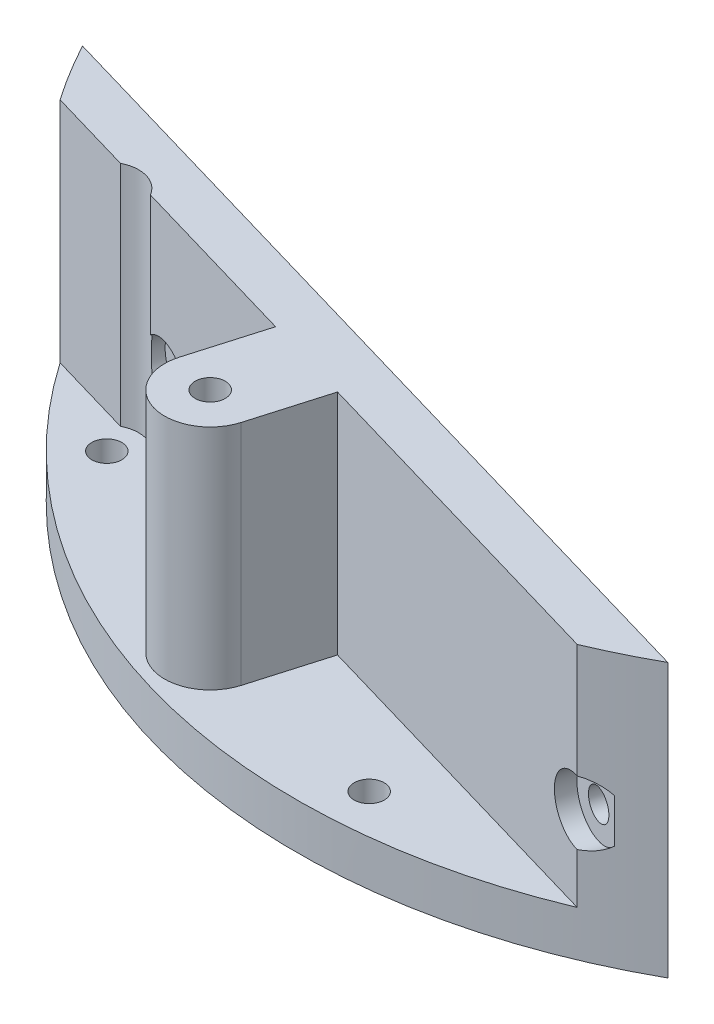
SolidWorks part; units mm, degrees
ref_plane "Front Plane" through (0, 0, 0) normal (0, 0, 1) x (1, 0, 0)
ref_plane "Top Plane" through (0, 0, 0) normal (0, 1, 0) x (1, 0, 0)
ref_plane "Right Plane" through (0, 0, 0) normal (1, 0, 0) x (0, 0, -1)
sketch "Sketch1" plane through (0, 0, 0) normal (0, 1, 0) x (1, 0, 0)
  line L0 (41.3804, -52.1206) -> (62.9195, 21.6805)
  line L1 (0, 0) -> (0, 66.55) construction
  line L2 (32.7481, -57.935) -> (-58.7697, -31.2253)
  line L3 (0, 0) -> (-47.058, -47.058) construction
  line L4 (0, 0) -> (0, -66.55) construction
  line L5 (0, 0) -> (3.483, -66.4588) construction
  circle A0 centre (0, 0) radius 66.55
  circle A2 centre (3.2213, -61.4656) radius 1.65
  circle A3 centre (-43.5224, -43.5224) radius 1.65
  dimension "D1" = 133.1
  dimension "D7" = 61.55
  dimension "D8" = 61.55
  dimension "D9" = 3.3
  dimension "D10" = 3.3
  dimension "D2" = 76.88
  dimension "D3" = 16.27
  dimension "D4" = 90
  dimension "D5" = 8
  dimension "D6" = 3
extrude "Boss-Extrude1" add sketch "Sketch1" along normal blind 5 contours L2 A0 A3 A2
sketch "Sketch2" plane through (0, 5, 0) normal (0, 1, 0) x (1, 0, 0)
  line L0 (-58.7697, -31.2253) -> (32.7481, -57.935)
  line L1 (-40.494, -41.7677) -> (26.121, -61.2095)
  line L2 (-54.9442, -37.5504) -> (-45.1316, -40.4143)
  arc A0 (26.121, -61.2095) -> (32.7481, -57.935) centre (0, 0) ccw
  arc A1 (-58.7697, -31.2253) -> (-54.9442, -37.5504) centre (0, 0) ccw
  arc A2 (-40.494, -41.7677) -> (-45.1316, -40.4143) centre (-43.5224, -43.5224) ccw
  dimension "D2" = 7
  dimension "D1" = 5
extrude "Boss-Extrude2" add sketch "Sketch2" along normal blind 25
sketch "Sketch3" plane through (-14.4116, 0, 49.3799) normal (-0.2802, 0, 0.96) x (0.96, 0, 0.2802)
  line L0 (42.2236, 30) -> (42.2236, 5) construction
  line L1 (47.6679, 0) -> (-47.6679, 0) construction
  circle A0 centre (41.5636, 14) radius 1.65
  circle A1 centre (-24.9364, 14) radius 1.65
  dimension "D1" = 0.66
  dimension "D2" = 3.3
  dimension "D3" = 3.3
  dimension "D4" = 14
  dimension "D5" = 14
  dimension "D6" = 67.16
extrude "Cut-Extrude1" cut sketch "Sketch3" against normal through all
sketch "Sketch4" plane through (-14.4116, 0, 49.3799) normal (-0.2802, 0, 0.96) x (0.96, 0, 0.2802)
  circle A0 centre (41.5636, 14) radius 3.5
  circle A1 centre (-24.9364, 14) radius 3.5
  dimension "D1" = 7
  dimension "D2" = 7
extrude "Cut-Extrude2" cut sketch "Sketch4" against normal blind 2
sketch "Sketch5" plane through (0, 0, 0) normal (0, -1, 0) x (1, 0, 0)
  circle A0 centre (0, 0) radius 66.25
  circle A3 centre (0, 0) radius 67.5
  dimension "D1" = 132.5
  dimension "D2" = 135
extrude "Cut-Extrude3" cut sketch "Sketch5" against normal through all
sketch "Sketch6" plane through (0, 0, 0) normal (0, 1, 0) x (1, 0, 0)
  line L0 (-23.4757, -55.6186) -> (-21.0864, -47.4319)
  line L1 (-40.494, -41.7677) -> (25.6655, -61.0765) construction
  line L2 (-13.8761, -58.4202) -> (-11.4868, -50.2335)
  line L3 (-40.494, -41.7677) -> (25.6655, -61.0765) construction
  line L4 (-21.0864, -47.4319) -> (-11.4868, -50.2335)
  line L5 (0, 0) -> (50000, 0) construction
  line L6 (-18.6759, -57.0194) -> (-16.2866, -48.8327) construction
  arc A0 (-23.4757, -55.6186) -> (-13.8761, -58.4202) centre (-18.6759, -57.0194) ccw
  circle A1 centre (-18.6759, -57.0194) radius 1.65
  dimension "D1" = 10
  dimension "D2" = 73.73
  dimension "D3" = 3.3
  dimension "D4" = 60
extrude "Boss-Extrude3" add sketch "Sketch6" along normal blind 30
sketch "Sketch7" plane through (0, 30, 0) normal (0, 1, 0) x (1, 0, 0)
  line L1 (-15.5358, -56.5472) -> (-17.5148, -54.0639)
  line L2 (-17.5148, -54.0639) -> (-20.6549, -54.5361)
  line L3 (-20.6549, -54.5361) -> (-21.816, -57.4916)
  line L4 (-21.816, -57.4916) -> (-19.837, -59.9749)
  line L5 (-19.837, -59.9749) -> (-16.6969, -59.5027)
  line L6 (-16.6969, -59.5027) -> (-15.5358, -56.5472)
  circle A0 centre (-18.6759, -57.0194) radius 2.75 construction
  dimension "D1" = 5.5
extrude "Cut-Extrude4" cut sketch "Sketch7" against normal blind 2.6 from offset 3
